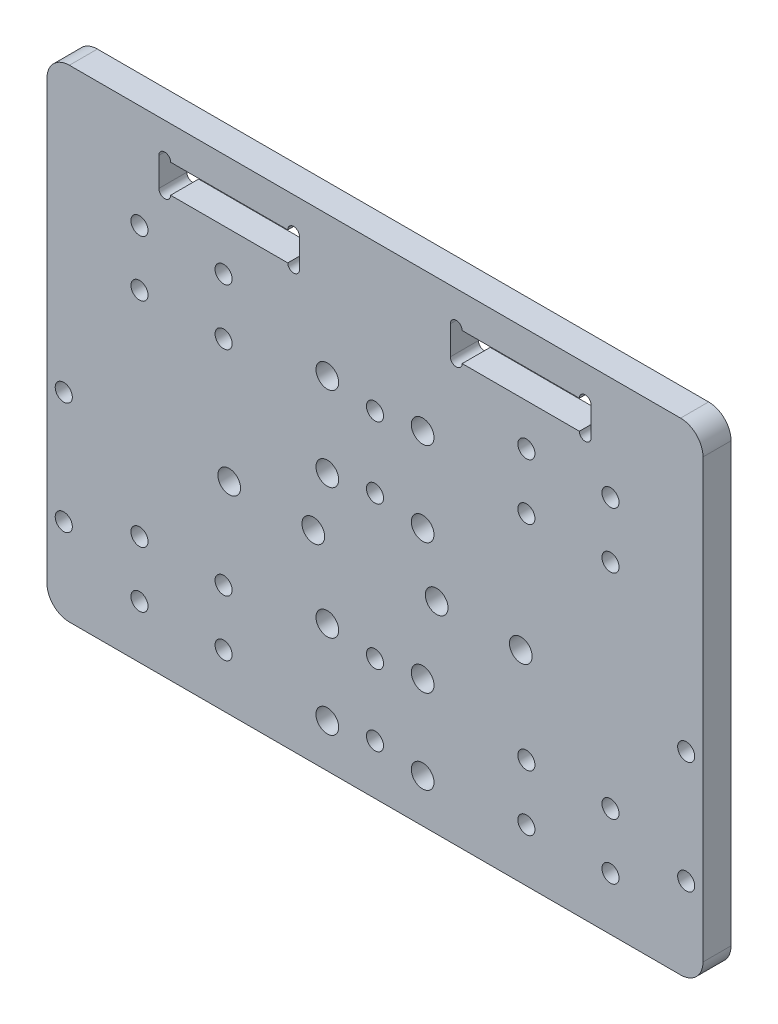
SolidWorks part; units mm, degrees
material "Thornel Mat VMA"
ref_plane "前视基准面" through (0, 0, 0) normal (0, 0, 1) x (1, 0, 0)
ref_plane "上视基准面" through (0, 0, 0) normal (0, 1, 0) x (1, 0, 0)
ref_plane "右视基准面" through (0, 0, 0) normal (1, 0, 0) x (0, 0, -1)
other "Configuration Table"
sketch "草图1" plane through (0, 0, 0) normal (0, 0, 1) x (1, 0, 0)
  line L1 (-58.5, -40) -> (58.5, -40)
  line L2 (-58.5, -40) -> (-58.5, 40)
  line L3 (-58.5, 40) -> (58.5, 40)
  line L4 (58.5, -40) -> (58.5, 40)
  line L5 (-58.5, -40) -> (58.5, 40) construction
  line L6 (-58.5, 40) -> (58.5, -40) construction
  point P0 (0, 0)
  dimension "D1" = 80
  dimension "D2" = 117
extrude "凸台-拉伸1" add sketch "草图1" along normal blind 5
sketch "草图2" plane through (0, 0, 5) normal (0, 0, 1) x (1, 0, 0)
  line L0 (-58.5, 40) -> (-58.5, -40) construction
  line L1 (-42, -30.55) -> (-27, -30.55) construction
  line L2 (-42, -30.55) -> (-42, -20.55) construction
  line L3 (-42, -20.55) -> (-27, -20.55) construction
  line L4 (-27, -30.55) -> (-27, -20.55) construction
  line L5 (-42, -30.55) -> (-27, -20.55) construction
  line L6 (-42, -20.55) -> (-27, -30.55) construction
  line L7 (-58.5, -40) -> (58.5, -40) construction
  line L8 (58.5, 40) -> (-58.5, 40) construction
  line L9 (-42, 17.5) -> (-27, 17.5) construction
  line L10 (-42, 17.5) -> (-42, 27.5) construction
  line L11 (-42, 27.5) -> (-27, 27.5) construction
  line L12 (-27, 17.5) -> (-27, 27.5) construction
  line L13 (-42, 17.5) -> (-27, 27.5) construction
  line L14 (-42, 27.5) -> (-27, 17.5) construction
  line L15 (0, 0) -> (0, 40) construction
  circle A0 centre (-27, -20.55) radius 1.525
  circle A1 centre (-42, -20.55) radius 1.525
  circle A2 centre (-42, -30.55) radius 1.525
  circle A3 centre (-27, -30.55) radius 1.525
  circle A4 centre (-42, 27.5) radius 1.525
  circle A5 centre (-42, 17.5) radius 1.525
  circle A6 centre (-27, 27.5) radius 1.525
  circle A7 centre (-27, 17.5) radius 1.525
  point P0 (-34.5, -25.55)
  point P14 (-34.5, 22.5)
  dimension "D3" = 3.05
  dimension "D6" = 3.05
  dimension "D1" = 15
  dimension "D2" = 10
  dimension "D4" = 16.5
  dimension "D5" = 9.45
  dimension "D7" = 12.5
  dimension "D8" = 10
extrude "切除-拉伸1" cut sketch "草图2" against normal blind 5
mirror "镜向1" about plane through (0, 0, 0) normal (1, 0, 0) of "切除-拉伸1"
sketch "草图3" plane through (0, 0, 5) normal (0, 0, 1) x (1, 0, 0)
  line L0 (58.5, 40) -> (-58.5, 40) construction
  line L1 (-8.5, 6) -> (8.5, 6) construction
  line L2 (-8.5, 6) -> (-8.5, 21) construction
  line L3 (-8.5, 21) -> (8.5, 21) construction
  line L4 (8.5, 6) -> (8.5, 21) construction
  line L5 (-8.5, 6) -> (8.5, 21) construction
  line L6 (-8.5, 21) -> (8.5, 6) construction
  circle A0 centre (-8.5, 21) radius 2.025
  circle A1 centre (8.5, 21) radius 2.025
  circle A2 centre (8.5, 6) radius 2.025
  circle A3 centre (-8.5, 6) radius 2.025
  point P0 (0, 13.5)
  dimension "D1" = 4.05
  dimension "D2" = 17
  dimension "D3" = 19
  dimension "D4" = 15
extrude "切除-拉伸2" cut sketch "草图3" against normal blind 5
sketch "草图4" plane through (0, 0, 5) normal (0, 0, 1) x (1, 0, 0)
  line L0 (-58.5, -40) -> (58.5, -40) construction
  line L1 (-8.5, -32.25) -> (8.5, -32.25) construction
  line L2 (-8.5, -32.25) -> (-8.5, -17.25) construction
  line L3 (-8.5, -17.25) -> (8.5, -17.25) construction
  line L4 (8.5, -32.25) -> (8.5, -17.25) construction
  line L5 (-8.5, -32.25) -> (8.5, -17.25) construction
  line L6 (-8.5, -17.25) -> (8.5, -32.25) construction
  circle A0 centre (8.5, -17.25) radius 2.025
  circle A1 centre (8.5, -32.25) radius 2.025
  circle A2 centre (-8.5, -32.25) radius 2.025
  circle A3 centre (-8.5, -17.25) radius 2.025
  point P0 (0, -24.75)
  dimension "D1" = 4.05
  dimension "D2" = 7.75
  dimension "D3" = 17
  dimension "D4" = 15
extrude "切除-拉伸3" cut sketch "草图4" against normal blind 5
sketch "草图5" plane through (0, 0, 5) normal (0, 0, 1) x (1, 0, 0)
  line L0 (-58.5, 40) -> (-58.5, -40) construction
  line L1 (-58.5, -40) -> (58.5, -40) construction
  circle A0 centre (-55.5, -5) radius 1.525
  circle A1 centre (-55.5, -25) radius 1.525
  dimension "D1" = 3.05
  dimension "D3" = 20
  dimension "D4" = 15
  dimension "D2" = 3
extrude "切除-拉伸4" cut sketch "草图5" against normal blind 5
mirror "镜向2" about plane through (0, 0, 0) normal (1, 0, 0) of "切除-拉伸4"
sketch "草图6" plane through (0, 0, 5) normal (0, 0, 1) x (1, 0, 0)
  line L0 (-8.5, 21) -> (-8.5, 6) construction
  line L1 (-8.5, 6) -> (-8.5, 13.5) construction
  line L2 (-8.5, 13.5) -> (0, 13.5) construction
  line L3 (0, 19.85) -> (0, 7.15) construction
  line L4 (-8.5, -32.25) -> (-8.5, -17.25) construction
  line L5 (0, -31.1) -> (0, -18.4) construction
  line L6 (0, -24.75) -> (-8.5, -24.75) construction
  circle A0 centre (0, 19.85) radius 1.525
  circle A1 centre (0, 7.15) radius 1.525
  circle A2 centre (0, -18.4) radius 1.525
  circle A3 centre (0, -31.1) radius 1.525
  dimension "D1" = 3.05
  dimension "D2" = 12.7
  dimension "D3" = 12.7
extrude "切除-拉伸5" cut sketch "草图6" against normal blind 5
sketch "草图7" plane through (0, 0, 5) normal (0, 0, 1) x (1, 0, 0)
  circle A0 centre (26, -4.05) radius 1.65 construction
  circle A1 centre (11, -4.05) radius 1.65 construction
  circle A2 centre (26, -4.05) radius 2.025
  circle A3 centre (11, -4.05) radius 2.025
  point P0 (26, -4.05)
  point P1 (11, -4.05)
  dimension "D1" = 4.05
extrude "切除-拉伸6" cut sketch "草图7" against normal blind 5
mirror "镜向4" about plane through (0, 0, 0) normal (1, 0, 0) of "切除-拉伸6"
sketch "草图9" plane through (0, 0, 5) normal (0, 0, 1) x (1, 0, 0)
  line L0 (-58.5, 40) -> (-58.5, -40) construction
  line L1 (58.5, 40) -> (-58.5, 40)
  line L2 (58.5, 40) -> (58.5, 46)
  line L3 (58.5, 46) -> (-58.5, 46)
  line L4 (-58.5, 40) -> (-58.5, 46)
  dimension "D1" = 6
extrude "凸台-拉伸2" add sketch "草图9" against normal blind 5
fillet "圆角2" radius 4 4 edges at (58.5, 46, 2.5) (-58.5, -40, 2.5) (58.5, -40, 2.5) (-58.5, 46, 2.5)
sketch "草图10" plane through (0, 0, 5) normal (0, 0, 1) x (1, 0, 0)
  line L0 (-58.5, 42) -> (-58.5, -36) construction
  line L1 (-38.55, 40.05) -> (-13.45, 40.05)
  line L2 (-38.55, 40.05) -> (-38.55, 34.95)
  line L3 (-38.55, 34.95) -> (-13.45, 34.95)
  line L4 (-13.45, 40.05) -> (-13.45, 34.95)
  line L5 (-38.55, 40.05) -> (-13.45, 34.95) construction
  line L6 (-38.55, 34.95) -> (-13.45, 40.05) construction
  line L8 (54.5, 46) -> (-54.5, 46) construction
  line L9 (-37.5, 40.05) -> (-37.5, 34.95) construction
  line L10 (-36.45, 40.05) -> (-36.45, 34.95)
  line L11 (-38.55, 40.05) -> (-38.55, 34.95)
  line L12 (-14.5, 40.05) -> (-14.5, 34.95) construction
  line L13 (-13.45, 40.05) -> (-13.45, 34.95)
  line L14 (-15.55, 40.05) -> (-15.55, 34.95)
  arc A0 (-36.45, 40.05) -> (-38.55, 40.05) centre (-37.5, 40.05) ccw
  arc A1 (-38.55, 34.95) -> (-36.45, 34.95) centre (-37.5, 34.95) ccw
  arc A2 (-13.45, 40.05) -> (-15.55, 40.05) centre (-14.5, 40.05) ccw
  arc A3 (-15.55, 34.95) -> (-13.45, 34.95) centre (-14.5, 34.95) ccw
  point P0 (-26, 37.5)
  point P11 (-37.5, 37.5)
  point P16 (-14.5, 37.5)
  dimension "D5" = 1.05
  dimension "D1" = 32.5
  dimension "D2" = 8.5
  dimension "D3" = 25.1
  dimension "D4" = 5.1
extrude "切除-拉伸7" cut sketch "草图10" against normal blind 5 contours L1 A0 | L14 L1 L10 L3 | L1 A2 | L1 L14 L3 L4 | L3 A3
mirror "镜向5" about plane through (0, 0, 0) normal (1, 0, 0) of "切除-拉伸7"
